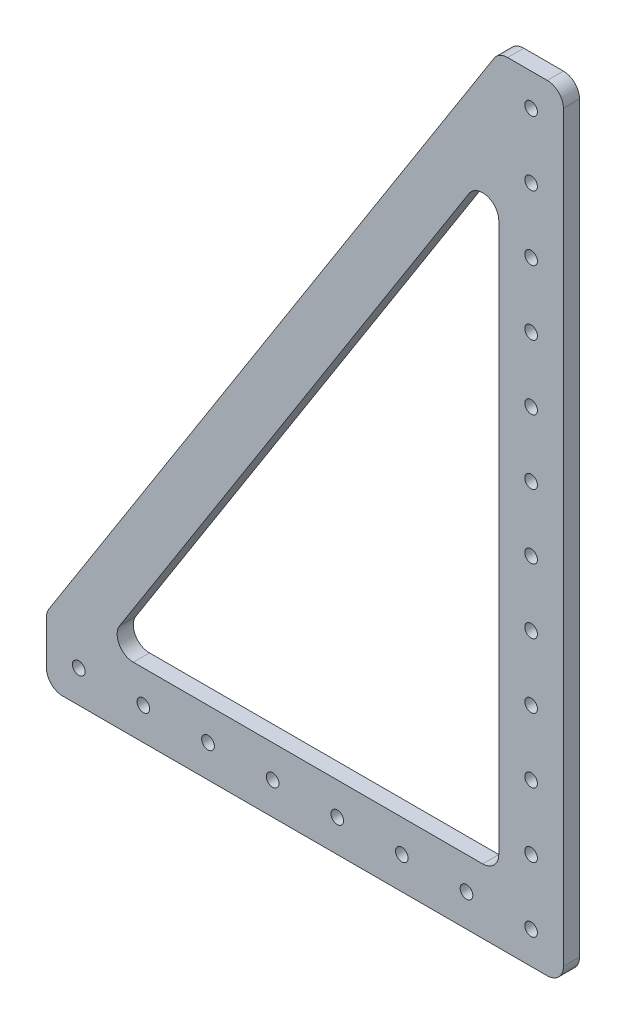
SolidWorks part; units mm, degrees
material "6061-T6 (SS)"
ref_plane "Front Plane" through (0, 0, 0) normal (0, 0, 1) x (1, 0, 0)
ref_plane "Top Plane" through (0, 0, 0) normal (0, 1, 0) x (1, 0, 0)
ref_plane "Right Plane" through (0, 0, 0) normal (1, 0, 0) x (0, 0, -1)
sketch "Sketch1" plane through (0, 0, 0) normal (0, 0, 1) x (1, 0, 0)
  line L0 (0, 25.4) -> (177.8, 304.8)
  line L1 (177.8, 304.8) -> (203.2, 304.8)
  line L2 (0, 25.4) -> (0, 0)
  line L3 (0, 0) -> (203.2, 0)
  line L4 (203.2, 304.8) -> (203.2, 0)
  dimension "D1" = 304.8
  dimension "D2" = 203.2
  dimension "D3" = 25.4
  dimension "D4" = 25.4
extrude "Boss-Extrude1" add sketch "Sketch1" along normal blind 6.35
sketch "Sketch2" plane through (0, 0, 6.35) normal (0, 0, 1) x (1, 0, 0)
  line L0 (0, 0) -> (203.2, 0) construction
  line L1 (203.2, 0) -> (203.2, 304.8) construction
  line L2 (22.5801, 25.4) -> (177.8, 25.4)
  line L3 (177.8, 25.4) -> (177.8, 269.3169)
  line L4 (177.8, 269.3169) -> (22.5801, 25.4)
  line L5 (177.8, 304.8) -> (0, 25.4) construction
  circle A0 centre (190.5, 12.7) radius 2.4892
  circle A1 centre (165.1, 12.7) radius 2.4892
  circle A2 centre (139.7, 12.7) radius 2.4892
  circle A3 centre (114.3, 12.7) radius 2.4892
  circle A4 centre (88.9, 12.7) radius 2.4892
  circle A5 centre (63.5, 12.7) radius 2.4892
  circle A6 centre (38.1, 12.7) radius 2.4892
  circle A67 centre (190.5, 38.1) radius 2.4892
  circle A68 centre (190.5, 63.5) radius 2.4892
  circle A69 centre (190.5, 88.9) radius 2.4892
  circle A70 centre (190.5, 114.3) radius 2.4892
  circle A71 centre (190.5, 139.7) radius 2.4892
  circle A72 centre (190.5, 165.1) radius 2.4892
  circle A73 centre (190.5, 190.5) radius 2.4892
  circle A74 centre (190.5, 215.9) radius 2.4892
  circle A75 centre (190.5, 241.3) radius 2.4892
  circle A76 centre (190.5, 266.7) radius 2.4892
  circle A161 centre (190.5, 292.1) radius 2.4892
  circle A233 centre (139.7, 38.1) radius 2.4892 construction
  circle A234 centre (114.3, 38.1) radius 2.4892 construction
  circle A235 centre (88.9, 38.1) radius 2.4892 construction
  circle A236 centre (63.5, 38.1) radius 2.4892 construction
  circle A237 centre (38.1, 38.1) radius 2.4892 construction
  circle A238 centre (165.1, 63.5) radius 2.4892 construction
  circle A239 centre (139.7, 63.5) radius 2.4892 construction
  circle A240 centre (114.3, 63.5) radius 2.4892 construction
  circle A241 centre (88.9, 63.5) radius 2.4892 construction
  circle A242 centre (63.5, 63.5) radius 2.4892 construction
  circle A243 centre (38.1, 63.5) radius 2.4892 construction
  circle A244 centre (165.1, 88.9) radius 2.4892 construction
  circle A245 centre (139.7, 88.9) radius 2.4892 construction
  circle A246 centre (114.3, 88.9) radius 2.4892 construction
  circle A247 centre (88.9, 88.9) radius 2.4892 construction
  circle A248 centre (63.5, 88.9) radius 2.4892 construction
  circle A249 centre (38.1, 88.9) radius 2.4892 construction
  circle A250 centre (165.1, 114.3) radius 2.4892 construction
  circle A251 centre (139.7, 114.3) radius 2.4892 construction
  circle A252 centre (114.3, 114.3) radius 2.4892 construction
  circle A253 centre (88.9, 114.3) radius 2.4892 construction
  circle A254 centre (63.5, 114.3) radius 2.4892 construction
  circle A255 centre (38.1, 114.3) radius 2.4892 construction
  circle A256 centre (165.1, 139.7) radius 2.4892 construction
  circle A257 centre (139.7, 139.7) radius 2.4892 construction
  circle A258 centre (114.3, 139.7) radius 2.4892 construction
  circle A259 centre (88.9, 139.7) radius 2.4892 construction
  circle A260 centre (63.5, 139.7) radius 2.4892 construction
  circle A261 centre (38.1, 139.7) radius 2.4892 construction
  circle A262 centre (165.1, 165.1) radius 2.4892 construction
  circle A263 centre (139.7, 165.1) radius 2.4892 construction
  circle A264 centre (114.3, 165.1) radius 2.4892 construction
  circle A265 centre (88.9, 165.1) radius 2.4892 construction
  circle A266 centre (63.5, 165.1) radius 2.4892 construction
  circle A267 centre (38.1, 165.1) radius 2.4892 construction
  circle A268 centre (165.1, 190.5) radius 2.4892 construction
  circle A269 centre (139.7, 190.5) radius 2.4892 construction
  circle A270 centre (114.3, 190.5) radius 2.4892 construction
  circle A271 centre (88.9, 190.5) radius 2.4892 construction
  circle A272 centre (63.5, 190.5) radius 2.4892 construction
  circle A273 centre (38.1, 190.5) radius 2.4892 construction
  circle A274 centre (165.1, 215.9) radius 2.4892 construction
  circle A275 centre (139.7, 215.9) radius 2.4892 construction
  circle A276 centre (114.3, 215.9) radius 2.4892 construction
  circle A277 centre (88.9, 215.9) radius 2.4892 construction
  circle A278 centre (63.5, 215.9) radius 2.4892 construction
  circle A279 centre (38.1, 215.9) radius 2.4892 construction
  circle A280 centre (165.1, 241.3) radius 2.4892 construction
  circle A281 centre (139.7, 241.3) radius 2.4892 construction
  circle A282 centre (114.3, 241.3) radius 2.4892 construction
  circle A283 centre (88.9, 241.3) radius 2.4892 construction
  circle A284 centre (63.5, 241.3) radius 2.4892 construction
  circle A285 centre (38.1, 241.3) radius 2.4892 construction
  circle A286 centre (165.1, 266.7) radius 2.4892 construction
  circle A287 centre (139.7, 266.7) radius 2.4892 construction
  circle A288 centre (114.3, 266.7) radius 2.4892 construction
  circle A289 centre (88.9, 266.7) radius 2.4892 construction
  circle A290 centre (63.5, 266.7) radius 2.4892 construction
  circle A291 centre (38.1, 266.7) radius 2.4892 construction
  circle A292 centre (165.1, 38.1) radius 2.4892 construction
  circle A293 centre (12.7, 12.7) radius 2.4892
  circle A477 centre (12.7, 38.1) radius 2.4892 [skipped]
  circle A485 centre (12.7, 63.5) radius 2.4892 [skipped]
  circle A493 centre (12.7, 88.9) radius 2.4892 [skipped]
  circle A501 centre (12.7, 114.3) radius 2.4892 [skipped]
  circle A509 centre (12.7, 139.7) radius 2.4892 [skipped]
  circle A517 centre (12.7, 165.1) radius 2.4892 [skipped]
  circle A525 centre (12.7, 190.5) radius 2.4892 [skipped]
  circle A533 centre (12.7, 215.9) radius 2.4892 [skipped]
  circle A541 centre (12.7, 241.3) radius 2.4892 [skipped]
  circle A549 centre (12.7, 266.7) radius 2.4892 [skipped]
  circle A557 centre (165.1, 292.1) radius 2.4892 [skipped]
  circle A558 centre (139.7, 292.1) radius 2.4892 [skipped]
  circle A559 centre (114.3, 292.1) radius 2.4892 [skipped]
  circle A560 centre (88.9, 292.1) radius 2.4892 [skipped]
  circle A561 centre (63.5, 292.1) radius 2.4892 [skipped]
  circle A562 centre (38.1, 292.1) radius 2.4892 [skipped]
  circle A563 centre (12.7, 292.1) radius 2.4892 [skipped]
  dimension "D1" = 12.7
  dimension "D2" = 12.7
  dimension "D3" = 4.9784
  dimension "D6" = 25.4
  dimension "D7" = 25.4
  dimension "D8" = 25.4
  dimension "D9" = 25.4
  dimension "D10" = 19.05
  dimension "D5" = 8
  dimension "D4" = 12
extrude "Cut-Extrude1" cut sketch "Sketch2" against normal through all
fillet "Fillet1" radius 6.35 8 edges at (203.2, 0, 3.175) (0, 25.4, 3.175) (177.8, 304.8, 3.175) (203.2, 304.8, 3.175) (0, 0, 3.175) (177.8, 25.4, 3.175) (177.8, 269.3169, 3.175) (22.5801, 25.4, 3.175)
